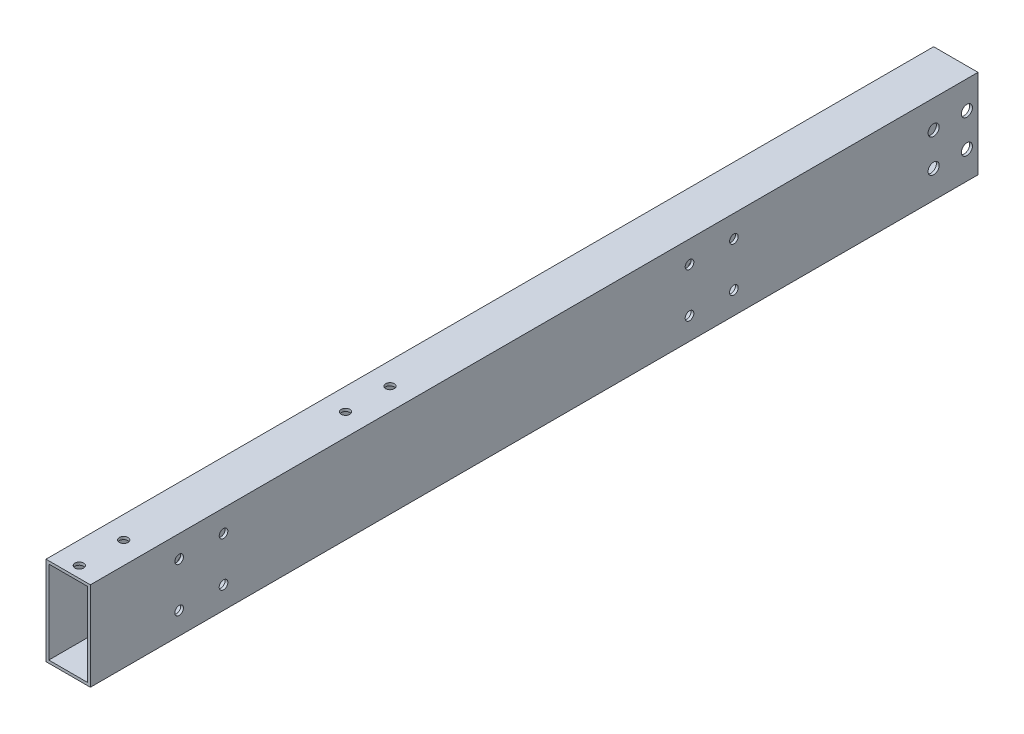
SolidWorks part; units mm, degrees
ref_plane "Front Plane" through (0, 0, 0) normal (0, 0, 1) x (1, 0, 0)
ref_plane "Top Plane" through (0, 0, 0) normal (0, 1, 0) x (1, 0, 0)
ref_plane "Right Plane" through (0, 0, 0) normal (1, 0, 0) x (0, 0, -1)
sketch "Sketch1" plane through (0, 0, 0) normal (0, 0, 1) x (1, 0, 0)
  line L1 (-12.7, -25.4) -> (12.7, -25.4)
  line L2 (-12.7, -25.4) -> (-12.7, 25.4)
  line L3 (-12.7, 25.4) -> (12.7, 25.4)
  line L4 (12.7, -25.4) -> (12.7, 25.4)
  line L5 (-12.7, -25.4) -> (12.7, 25.4) construction
  line L6 (-12.7, 25.4) -> (12.7, -25.4) construction
  point P0 (0, 0)
  dimension "D1" = 50.8
  dimension "D2" = 25.4
extrude "Extrude-Thin1" add sketch "Sketch1" along normal blind 508 thin thin type one direction reverse wall 1.5875
sketch "Sketch2" plane through (12.7, 0, 0) normal (1, 0, 0) x (0, 0, -1)
  circle A0 centre (-457.2, 12.7) radius 2.4765
  circle A1 centre (-431.8, 12.7) radius 2.4765
  circle A2 centre (-431.8, -12.7) radius 2.4765
  circle A3 centre (-457.2, -12.7) radius 2.4765
  circle A4 centre (-165.1, 12.7) radius 2.4765
  circle A5 centre (-139.7, 12.7) radius 2.4765
  circle A6 centre (-139.7, -12.7) radius 2.4765
  circle A7 centre (-165.1, -12.7) radius 2.4765
extrude "Cut-Extrude1" cut sketch "Sketch2" against normal through all
sketch "Sketch3" plane through (0, 25.4, 0) normal (0, 1, 0) x (1, 0, 0)
  circle A0 centre (0, -323.85) radius 2.4892 construction
  circle A1 centre (0, -349.25) radius 2.4892 construction
  circle A2 centre (0, -476.25) radius 2.4892 construction
  circle A3 centre (0, -501.65) radius 2.4892 construction
  circle A4 centre (0, -323.85) radius 2.4892
  circle A5 centre (0, -349.25) radius 2.4892
  circle A6 centre (0, -476.25) radius 2.4892
  circle A7 centre (0, -501.65) radius 2.4892
extrude "Cut-Extrude2" cut sketch "Sketch3" against normal up to next
sketch "Sketch4" plane through (12.7, 0, 0) normal (1, 0, 0) x (0, 0, -1)
  line L0 (-508, -25.4) -> (0, -25.4) construction
  line L1 (-25.4, -9.525) -> (-6.35, -9.525) construction
  line L2 (-25.4, -9.525) -> (-25.4, 9.525) construction
  line L3 (-25.4, 9.525) -> (-6.35, 9.525) construction
  line L4 (-6.35, -9.525) -> (-6.35, 9.525) construction
  line L5 (-25.4, -9.525) -> (-6.35, 9.525) construction
  line L6 (-25.4, 9.525) -> (-6.35, -9.525) construction
  line L8 (0, -25.4) -> (0, 25.4) construction
  circle A0 centre (-25.4, 9.525) radius 3.175
  circle A1 centre (-6.35, 9.525) radius 3.175
  circle A2 centre (-6.35, -9.525) radius 3.175
  circle A3 centre (-25.4, -9.525) radius 3.175
  point P0 (-15.875, 0)
  point P11 (0, 0)
  dimension "D1" = 6.35
  dimension "D2" = 25.4
  dimension "D3" = 6.35
  dimension "D4" = 19.05
  dimension "D5" = 19.05
extrude "Cut-Extrude3" cut sketch "Sketch4" against normal up to next
